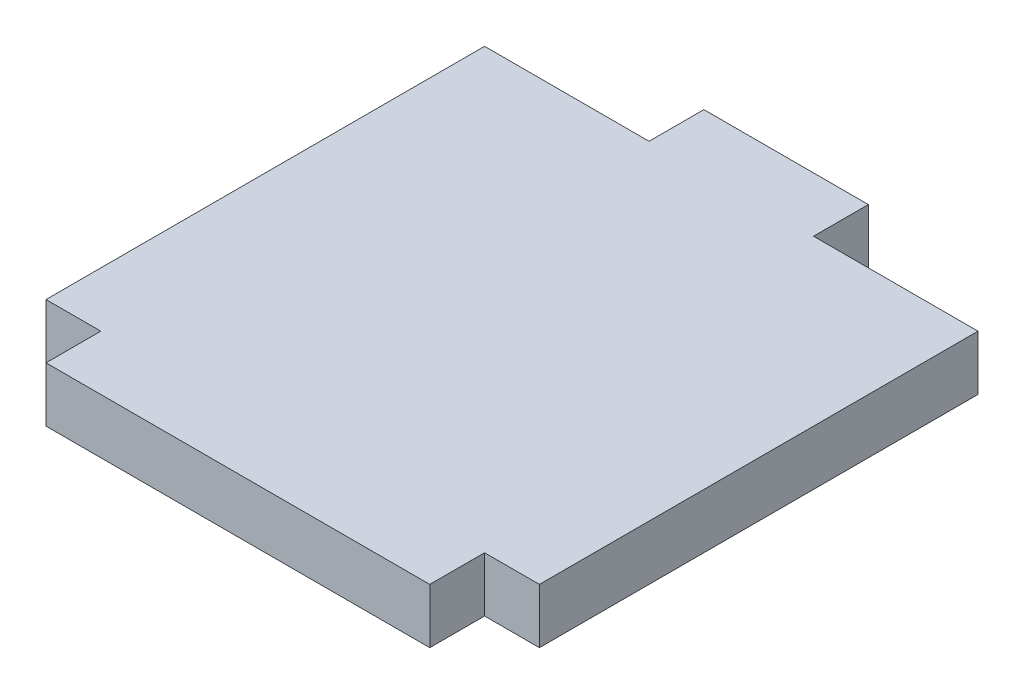
SolidWorks part; units mm, degrees
ref_plane "前视基准面" through (0, 0, 0) normal (0, 0, 1) x (1, 0, 0)
ref_plane "上视基准面" through (0, 0, 0) normal (0, 1, 0) x (1, 0, 0)
ref_plane "右视基准面" through (0, 0, 0) normal (1, 0, 0) x (0, 0, -1)
sketch "草图1" plane through (0, 0, 0) normal (0, 1, 0) x (1, 0, 0)
  line L1 (-22.5, -20) -> (22.5, -20)
  line L2 (-22.5, -20) -> (-22.5, 20)
  line L3 (-22.5, 20) -> (22.5, 20)
  line L4 (22.5, -20) -> (22.5, 20)
  line L5 (-22.5, -20) -> (22.5, 20) construction
  line L6 (-22.5, 20) -> (22.5, -20) construction
  line L7 (-17.5, -20) -> (17.5, -20)
  line L8 (-17.5, -20) -> (-17.5, -25)
  line L9 (-17.5, -25) -> (17.5, -25)
  line L10 (17.5, -20) -> (17.5, -25)
  point P0 (0, 0)
  dimension "D1" = 45
  dimension "D2" = 40
  dimension "D3" = 5
  dimension "D4" = 5
  dimension "D5" = 5
extrude "凸台-拉伸1" add sketch "草图1" along normal blind 5 contours L1 L4 L3 L2 | L10 L1 L8 L9
sketch "草图2" plane through (0, 5, 0) normal (0, 1, 0) x (1, 0, 0)
  line L0 (-22.5, 20) -> (22.5, 20) construction
  line L1 (-7.5, 20) -> (7.5, 20)
  line L2 (-7.5, 20) -> (-7.5, 25)
  line L3 (-7.5, 25) -> (7.5, 25)
  line L4 (7.5, 20) -> (7.5, 25)
  line L5 (-22.5, -20) -> (-22.5, 20) construction
  line L6 (22.5, -20) -> (22.5, 20) construction
  dimension "D1" = 15
  dimension "D2" = 15
  dimension "D3" = 5
extrude "凸台-拉伸2" add sketch "草图2" against normal blind 5
